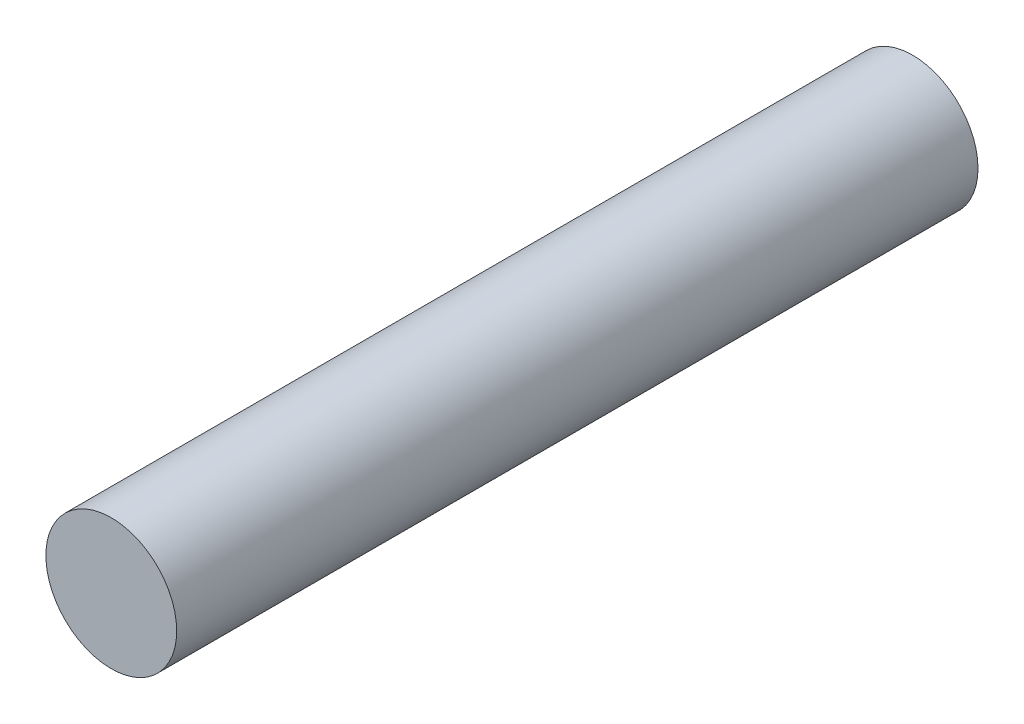
SolidWorks part; units mm, degrees
material "AISI 316 Annealed Stainless Steel Bar (SS)"
ref_plane "Front Plane" through (0, 0, 0) normal (0, 0, 1) x (1, 0, 0)
ref_plane "Top Plane" through (0, 0, 0) normal (0, 1, 0) x (1, 0, 0)
ref_plane "Right Plane" through (0, 0, 0) normal (1, 0, 0) x (0, 0, -1)
sketch "Sketch1" plane through (0, 0, 0) normal (0, 0, 1) x (1, 0, 0)
  circle A0 centre (0, 0) radius 4
  dimension "D1" = 8
extrude "Boss-Extrude1" add sketch "Sketch1" along normal blind 49
sketch "Sketch3" plane through (0, 0, 0) normal (0, 0, 1) x (1, 0, 0)
  line L0 (2.5981, -1.5) -> (-2.5981, -1.5)
  arc A0 (-2.5981, -1.5) -> (2.5981, -1.5) centre (0, 0) ccw
  dimension "D1" = 6
  dimension "D2" = 1.5
sketch "Sketch4" plane through (0, 0, 49) normal (0, 0, 1) x (1, 0, 0)
  line L0 (-2.5981, -1.5) -> (2.5981, -1.5)
  arc A0 (-2.5981, -1.5) -> (2.5981, -1.5) centre (0, 0) ccw
  dimension "D1" = 6
  dimension "D2" = 1.5
